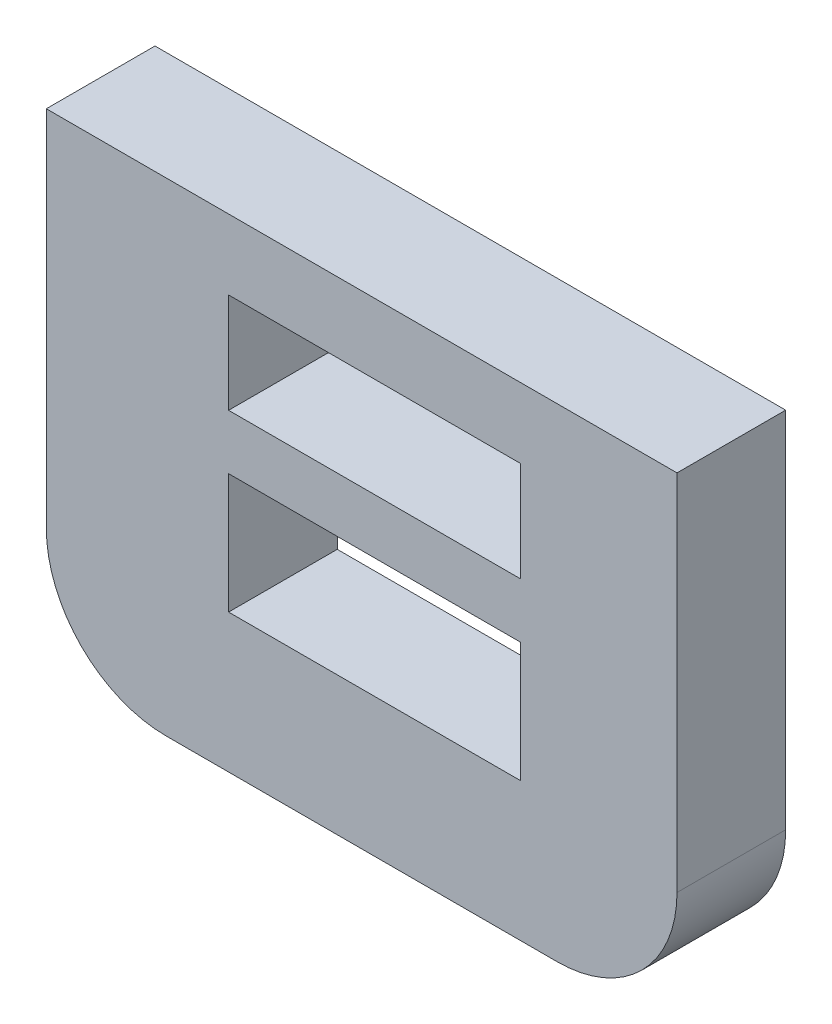
SolidWorks part; units mm, degrees
ref_plane "Front Plane" through (0, 0, 0) normal (0, 0, 1) x (1, 0, 0)
ref_plane "Top Plane" through (0, 0, 0) normal (0, 1, 0) x (1, 0, 0)
ref_plane "Right Plane" through (0, 0, 0) normal (1, 0, 0) x (0, 0, -1)
sketch "Sketch1" plane through (0, 0, 0) normal (0, 0, 1) x (1, 0, 0)
  line L8 (-33.4727, -411.0557) -> (-33.4727, -414.0557)
  line L9 (-26.1675, -411.0557) -> (-33.4727, -411.0557)
  line L10 (-26.1675, -414.0557) -> (-26.1675, -411.0557)
  line L11 (-33.4727, -414.0557) -> (-26.1675, -414.0557)
  line L15 (-26.1675, -409.6829) -> (-33.4727, -409.6829)
  line L16 (-26.1675, -407.1829) -> (-33.4727, -407.1829)
  line L17 (-26.1675, -409.6829) -> (-26.1675, -407.1829)
  line L19 (-33.4727, -407.1829) -> (-33.4727, -409.6829)
  line L25 (-25.2522, -417.522) -> (-35.0338, -417.522)
  line L26 (-38.0338, -414.522) -> (-38.0338, -405.4286)
  line L27 (-22.2522, -405.4286) -> (-22.2522, -414.522)
  line L28 (-38.0338, -405.4286) -> (-22.2522, -405.4286)
  arc A2 (-38.0338, -414.522) -> (-35.0338, -417.522) centre (-35.0338, -414.522) ccw
  arc A3 (-25.2522, -417.522) -> (-22.2522, -414.522) centre (-25.2522, -414.522) ccw
extrude "Boss-Extrude1" add sketch "Sketch1" along normal up to surface (2.7194 mm away)
